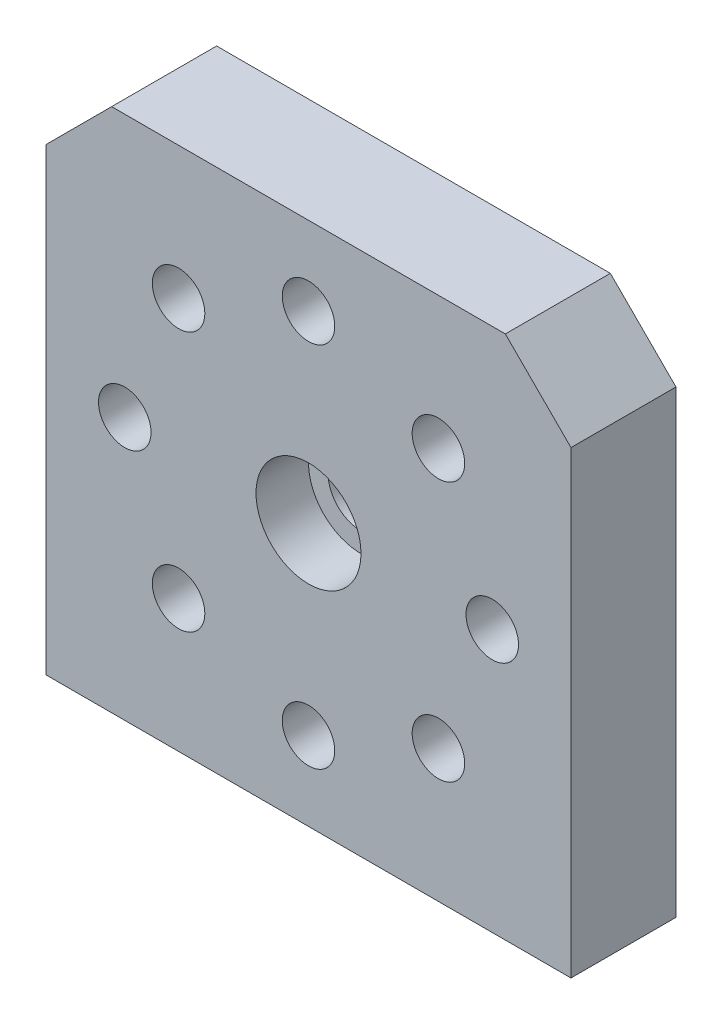
SolidWorks part; units mm, degrees
ref_plane "Plan de face" through (0, 0, 0) normal (0, 0, 1) x (1, 0, 0)
ref_plane "Plan de dessus" through (0, 0, 0) normal (0, 1, 0) x (1, 0, 0)
ref_plane "Plan de droite" through (0, 0, 0) normal (1, 0, 0) x (0, 0, -1)
sketch "Esquisse1" plane through (0, 0, 0) normal (0, 0, 1) x (1, 0, 0)
  line L0 (-20, -20) -> (-20, 15)
  line L1 (-15, 20) -> (15, 20)
  line L2 (20, 15) -> (20, -20)
  line L3 (20, -20) -> (-20, -20)
  line L4 (15, 20) -> (20, 15)
  line L6 (-15, 20) -> (-20, 15)
  circle A0 centre (0, 0) radius 2.5
  circle A1 centre (9.8995, 9.8995) radius 2
  circle A2 centre (0, 14) radius 2
  circle A3 centre (14, 0) radius 2
  circle A4 centre (9.8995, -9.8995) radius 2
  circle A5 centre (0, -14) radius 2
  circle A6 centre (-9.8995, -9.8995) radius 2
  circle A7 centre (-14, 0) radius 2
  circle A8 centre (-9.8995, 9.8995) radius 2
extrude "Extrusion1" add sketch "Esquisse1" along normal blind 8
sketch "Esquisse2" plane through (0, 0, 8) normal (0, 0, 1) x (1, 0, 0)
  circle A0 centre (0, 0) radius 4
extrude "Extrusion2" cut sketch "Esquisse2" against normal blind 4
sketch "Esquisse3" plane through (0, -20, 0) normal (0, -1, 0) x (1, 0, 0)
  line L0 (-20, 8) -> (-20, 0) construction
  line L2 (-20, 4) -> (20, 4) construction
  line L4 (20, 8) -> (20, 0) construction
  circle A1 centre (-15.5, 4) radius 2
  circle A2 centre (15.5, 4) radius 2
extrude "Extrusion3" cut sketch "Esquisse3" against normal blind 15
